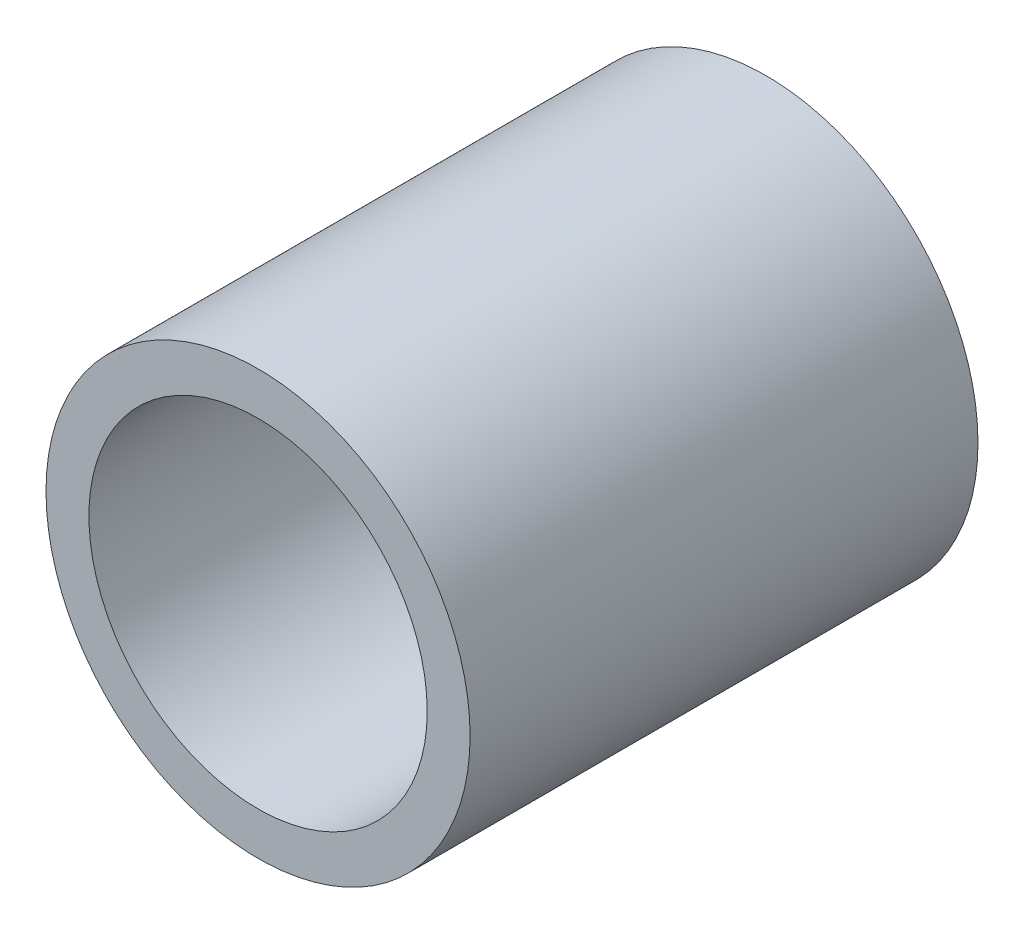
SolidWorks part; units mm, degrees
ref_plane "Front Plane" through (0, 0, 0) normal (0, 0, 1) x (1, 0, 0)
ref_plane "Top Plane" through (0, 0, 0) normal (0, 1, 0) x (1, 0, 0)
ref_plane "Right Plane" through (0, 0, 0) normal (1, 0, 0) x (0, 0, -1)
sketch "Sketch1" plane through (0, 0, 0) normal (0, 0, 1) x (1, 0, 0)
  circle A0 centre (0, 0) radius 16.7005
  dimension "Pipe OD" = 33.401
extrude "Extrude-Thin1" add sketch "Sketch1" along normal mid plane 40 thin thin type one direction reverse wall 3.3782
